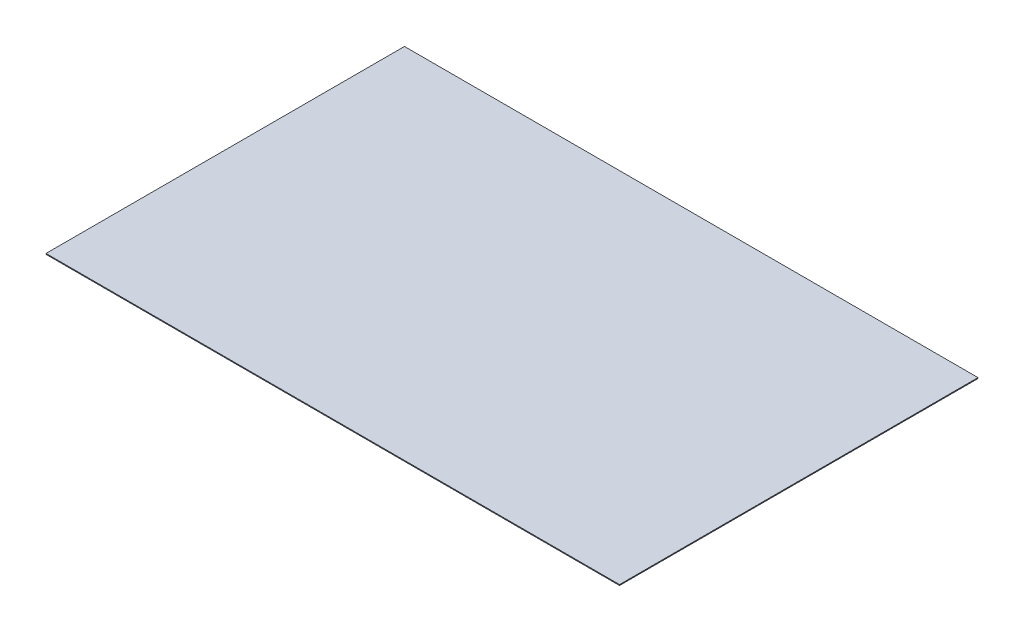
SolidWorks part; units mm, degrees
material "AISI 304"
ref_plane "Front Plane" through (0, 0, 0) normal (0, 0, 1) x (1, 0, 0)
ref_plane "Top Plane" through (0, 0, 0) normal (0, 1, 0) x (1, 0, 0)
ref_plane "Right Plane" through (0, 0, 0) normal (1, 0, 0) x (0, 0, -1)
sketch "Sketch1" plane through (0, 0, 0) normal (0, 0, 1) x (1, 0, 0)
  line L0 (-203.2, 0) -> (203.2, 0) construction
  line L1 (0, -0.3048) -> (0, 0.3048) construction
  point P5 (0, 0)
  point P9 (0, 0)
  dimension "Width" = 406.4
  dimension "Thickness" = 0.6096
sketch "Sketch2" plane through (0, 0, 0) normal (1, 0, 0) x (0, 0, -1)
  line L0 (-127, 0) -> (127, 0) construction
  point P3 (0, 0)
  dimension "Length" = 254
sketch "Sketch3" plane through (0, 0, 0) normal (0, 0, 1) x (1, 0, 0)
  line L1 (-203.2, -0.3048) -> (203.2, -0.3048)
  line L2 (-203.2, -0.3048) -> (-203.2, 0.3048)
  line L3 (-203.2, 0.3048) -> (203.2, 0.3048)
  line L4 (203.2, -0.3048) -> (203.2, 0.3048)
  line L5 (-203.2, -0.3048) -> (203.2, 0.3048) construction
  line L6 (-203.2, 0.3048) -> (203.2, -0.3048) construction
  point P0 (0, 0)
extrude "Boss-Extrude1" add sketch "Sketch3" along normal mid plane 254
sketch "Sketch4" plane through (0, 0, 0) normal (0, 1, 0) x (1, 0, 0)
  line L0 (-203.2, 0) -> (-96.139, 0)
  line L1 (96.139, 0) -> (203.2, 0)
  line L2 (0, 127) -> (0, 19.939)
  line L3 (0, -19.939) -> (0, -127)
  point P6 (203.2, -127)
  point P9 (-203.2, 127)
  point P10 (-96.139, 0)
  point P11 (0, -19.939)
  point P12 (96.139, 0)
  point P13 (203.2, 127)
  point P22 (0, 19.939)
  dimension "D1" = 107.061
sketch "Sketch5" plane through (0, 0, 0) normal (1, 0, 0) x (0, 0, -1)
  point P0 (127, 0.3048)
  point P1 (127, -0.3048)
equation "\"D1@Boss-Extrude1\"=\"Length@Sketch2\""
